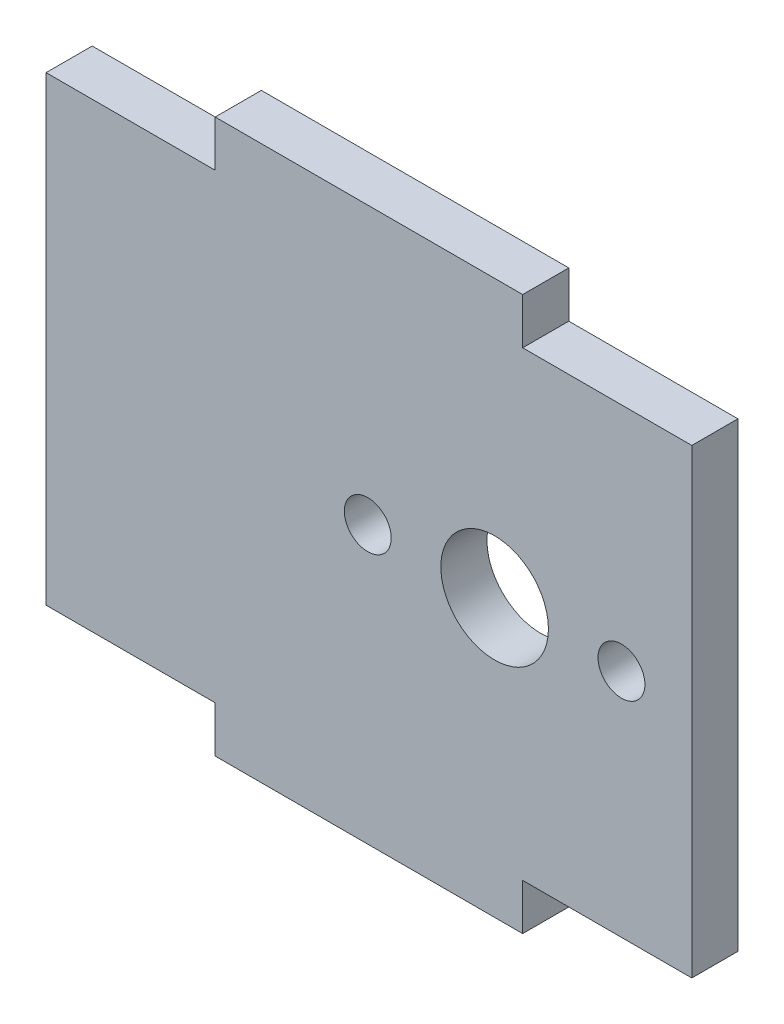
SolidWorks part; units mm, degrees
material "Acrylic (Medium-high impact)"
ref_plane "Front Plane" through (0, 0, 0) normal (0, 0, 1) x (1, 0, 0)
ref_plane "Top Plane" through (0, 0, 0) normal (0, 1, 0) x (1, 0, 0)
ref_plane "Right Plane" through (0, 0, 0) normal (1, 0, 0) x (0, 0, -1)
sketch "Sketch1" plane through (0, 0, 0) normal (0, 0, 1) x (1, 0, 0)
  line L0 (0, 0) -> (14.7677, 0) construction
  line L1 (-21, 15) -> (21, 15)
  line L2 (-21, 15) -> (-21, -15)
  line L3 (-21, -15) -> (21, -15)
  line L4 (21, 15) -> (21, -15)
  line L5 (-21, 15) -> (21, -15) construction
  line L6 (-21, -15) -> (21, 15) construction
  line L7 (-10, 15) -> (10, 15)
  line L8 (-10, 15) -> (-10, 18)
  line L9 (-10, 18) -> (10, 18)
  line L10 (10, 15) -> (10, 18)
  line L11 (10, -15) -> (10, -18)
  line L12 (-10, -18) -> (10, -18)
  line L13 (-10, -15) -> (-10, -18)
  line L14 (-10, -15) -> (10, -15)
  point P0 (0, 0)
  point P10 (0, 18)
  dimension "D1" = 42
  dimension "D2" = 30
  dimension "D3" = 3
  dimension "D4" = 20
extrude "Boss-Extrude1" add sketch "Sketch1" along normal blind 3 contours L4 L1 L2 L3 | L1 L10 L9 L8 | L3 L13 L12 L11
sketch "Sketch2" plane through (0, 0, 3) normal (0, 0, 1) x (1, 0, 0)
  line L0 (21, 15) -> (21, -15) construction
  circle A0 centre (8.175, 0) radius 3.5
  circle A1 centre (16.425, 0) radius 1.525
  circle A2 centre (-0.075, 0) radius 1.525
  dimension "D1" = 7
  dimension "D2" = 3.05
  dimension "D3" = 3.05
  dimension "D4" = 16.5
  dimension "D5" = 8.25
  dimension "D6" = 4.575
extrude "Cut-Extrude1" cut sketch "Sketch2" against normal through all
